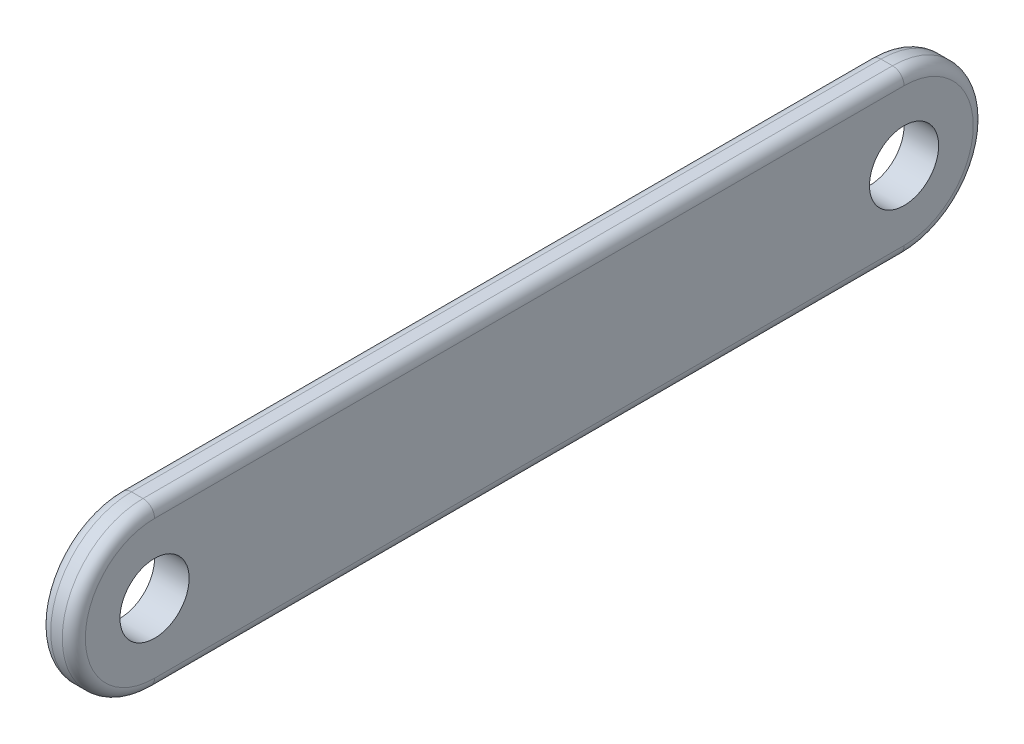
SolidWorks part; units mm, degrees
ref_plane "前视基准面" through (0, 0, 0) normal (0, 0, 1) x (1, 0, 0)
ref_plane "上视基准面" through (0, 0, 0) normal (0, 1, 0) x (1, 0, 0)
ref_plane "右视基准面" through (0, 0, 0) normal (1, 0, 0) x (0, 0, -1)
sketch "草图1" plane through (0, 0, 0) normal (1, 0, 0) x (0, 0, -1)
  line L0 (-32.5, 0) -> (32.5, 0) construction
  line L1 (-32.5, 7) -> (32.5, 7)
  line L2 (-32.5, -7) -> (32.5, -7)
  arc A0 (-32.5, 7) -> (-32.5, -7) centre (-32.5, 0) ccw
  arc A1 (32.5, -7) -> (32.5, 7) centre (32.5, 0) ccw
  circle A2 centre (-32.5, 0) radius 3
  circle A3 centre (32.5, 0) radius 3
  point P2 (0, 0)
  dimension "D2" = 7
  dimension "D3" = 6
  dimension "D1" = 65
extrude "凸台-拉伸1" add sketch "草图1" along normal blind 3
fillet "圆角1" radius 1 8 edges at (0, 0, -39.5) (0, -7, 0) (0, 0, 39.5) (3, 0, -39.5) (3, -7, 0) (3, 0, 39.5) (0, 7, 0) (3, 7, 0)
